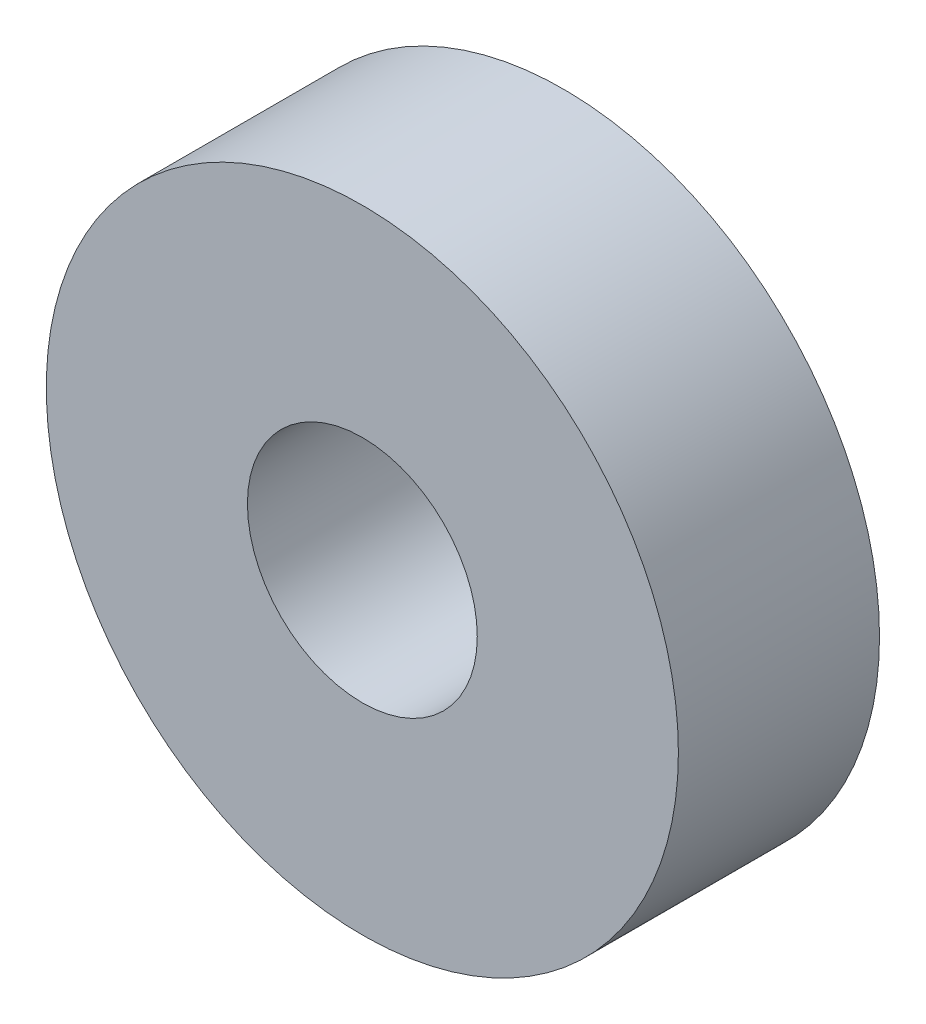
SolidWorks part; units mm, degrees
ref_plane "Front Plane" through (0, 0, 0) normal (0, 0, 1) x (1, 0, 0)
ref_plane "Top Plane" through (0, 0, 0) normal (0, 1, 0) x (1, 0, 0)
ref_plane "Right Plane" through (0, 0, 0) normal (1, 0, 0) x (0, 0, -1)
sketch "Sketch1" plane through (0, 0, 0) normal (0, 0, 1) x (1, 0, 0)
  circle A0 centre (0, 0) radius 11
  dimension "D1" = 22
extrude "Extrude1" add sketch "Sketch1" along normal blind 7
sketch "Sketch2" plane through (0, 0, 7) normal (0, 0, 1) x (1, 0, 0)
  circle A0 centre (0, 0) radius 4
  dimension "D1" = 8
extrude "Extrude2" cut sketch "Sketch2" against normal through all
